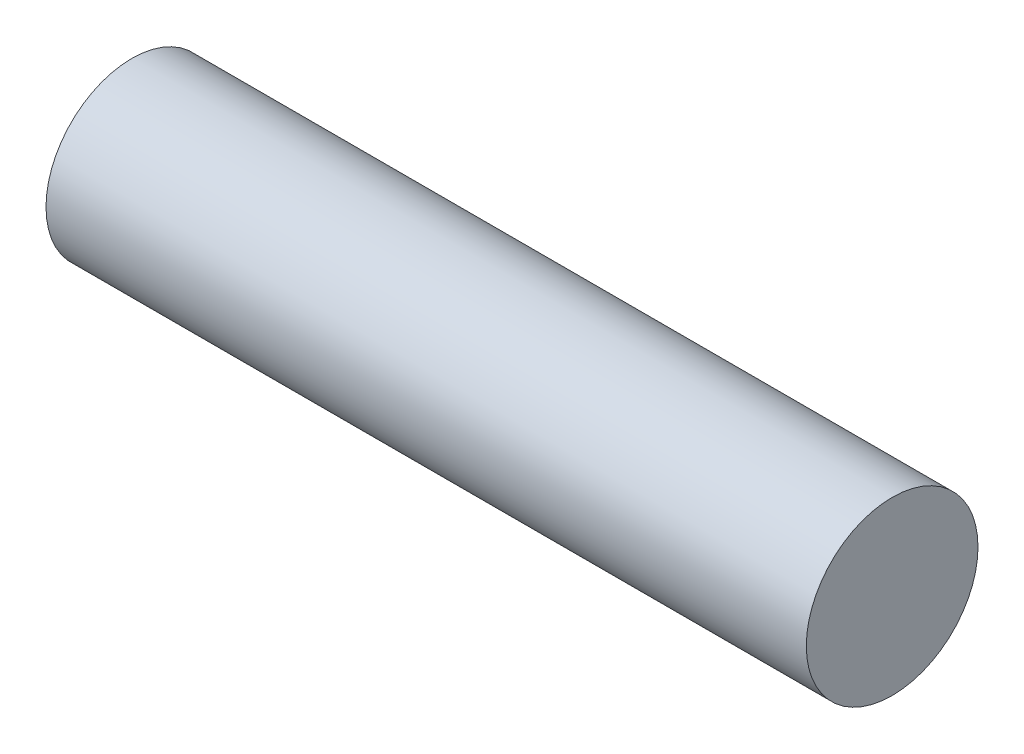
SolidWorks part; units mm, degrees
material "Alloy Steel"
ref_plane "Front Plane" through (0, 0, 0) normal (0, 0, 1) x (1, 0, 0)
ref_plane "Top Plane" through (0, 0, 0) normal (0, 1, 0) x (1, 0, 0)
ref_plane "Right Plane" through (0, 0, 0) normal (1, 0, 0) x (0, 0, -1)
sketch "Sketch1" plane through (0, 0, 0) normal (1, 0, 0) x (0, 0, -1)
  circle A0 centre (0, 0) radius 1.778
  dimension "D1" = 3.556
extrude "Boss-Extrude1" add sketch "Sketch1" along normal mid plane 15.748
